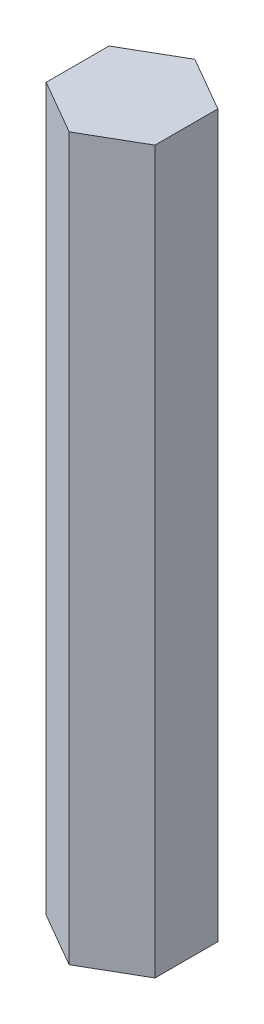
SolidWorks part; units mm, degrees
material "Chrome Stainless Steel"
ref_plane "Front Plane" through (0, 0, 0) normal (0, 0, 1) x (1, 0, 0)
ref_plane "Top Plane" through (0, 0, 0) normal (0, 1, 0) x (1, 0, 0)
ref_plane "Right Plane" through (0, 0, 0) normal (1, 0, 0) x (0, 0, -1)
sketch "Sketch1" plane through (0, 0, 0) normal (0, 1, 0) x (1, 0, 0)
  line L1 (1.2648, 5.1118) -> (-1.2648, 3.6513)
  line L2 (-1.2648, 3.6513) -> (-1.2648, 0.7302)
  line L3 (-1.2648, 0.7302) -> (1.2648, -0.7302)
  line L4 (1.2648, -0.7302) -> (3.7945, 0.7302)
  line L5 (3.7945, 0.7302) -> (3.7945, 3.6513)
  line L6 (3.7945, 3.6513) -> (1.2648, 5.1118)
extrude "Boss-Extrude1" add sketch "Sketch1" along normal blind 33.528
